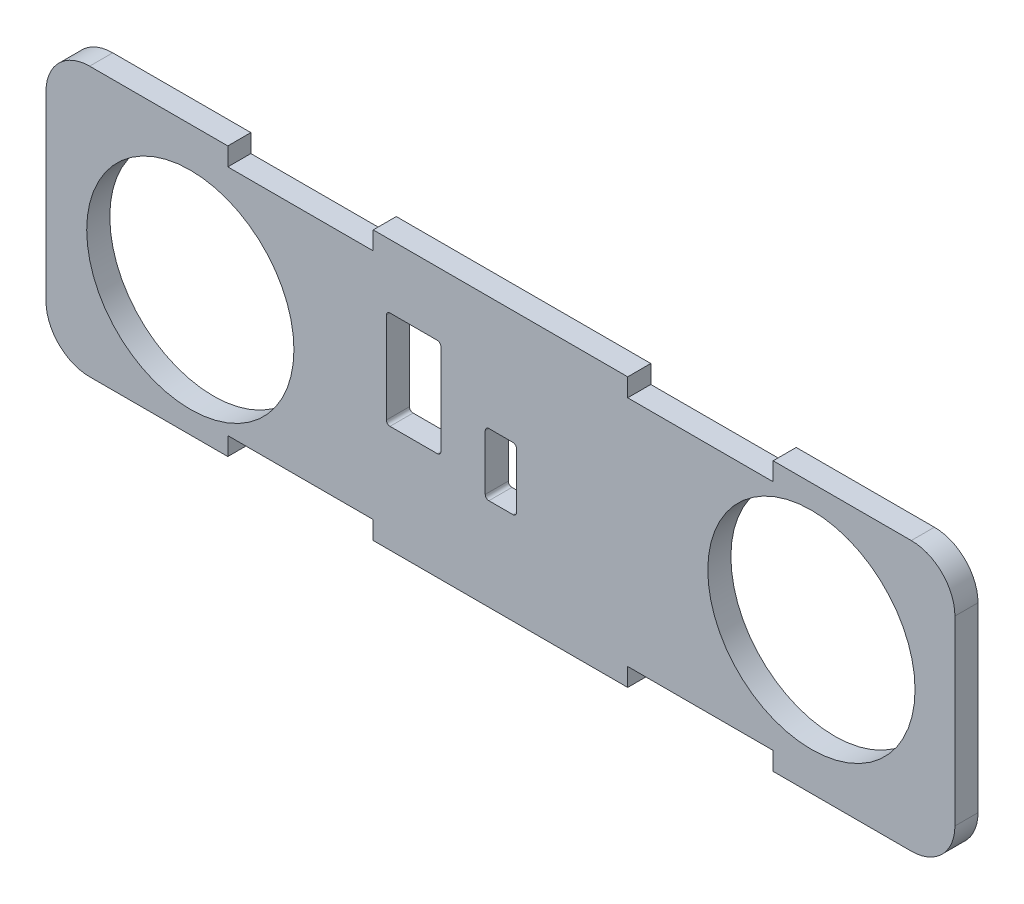
SolidWorks part; units mm, degrees
ref_plane "Front" through (0, 0, 0) normal (0, 0, 1) x (1, 0, 0)
ref_plane "Top" through (0, 0, 0) normal (0, 1, 0) x (1, 0, 0)
ref_plane "Right" through (0, 0, 0) normal (1, 0, 0) x (0, 0, -1)
sketch "Sketch1" plane through (0, 0, 0) normal (0, 0, 1) x (1, 0, 0)
  line L1 (-62.5, -18.5) -> (62.5, -18.5)
  line L2 (-62.5, -18.5) -> (-62.5, 18.5)
  line L3 (-62.5, 18.5) -> (62.5, 18.5)
  line L4 (62.5, -18.5) -> (62.5, 18.5)
  line L5 (-62.5, -18.5) -> (62.5, 18.5) construction
  line L6 (-62.5, 18.5) -> (62.5, -18.5) construction
  point P0 (0, 0)
  dimension "D1" = 37
  dimension "D2" = 125
extrude "Boss-Extrude1" add sketch "Sketch1" along normal blind 3.175
fillet "Fillet1" radius 6 4 edges at (-62.5, 18.5, 1.5875) (62.5, 18.5, 1.5875) (62.5, -18.5, 1.5875) (-62.5, -18.5, 1.5875)
sketch "Sketch2" plane through (0, 0, 3.175) normal (0, 0, 1) x (1, 0, 0)
  line L4 (-2.0937, 2.7963) -> (-1.3697, 2.7963) construction
  line L5 (2.2063, -5.8037) -> (1.4823, -5.8037) construction
  line L6 (2.2063, -5.8037) -> (2.2063, -5.4037) construction
  line L7 (-2.0937, 2.7963) -> (-2.0937, 2.3963) construction
  line L8 (-9.9037, -0.7737) -> (-13.9837, -0.7737) construction
  line L9 (-13.9837, 6.8463) -> (-9.9037, 6.8463) construction
  line L10 (-14.4837, 4.8063) -> (-14.4837, 6.3463) construction
  line L11 (-9.4037, 1.2663) -> (-9.4037, -0.2737) construction
  line L12 (-9.9037, -0.7737) -> (-13.9837, -0.7737) construction
  line L13 (-13.9837, 6.8463) -> (-9.9037, 6.8463) construction
  line L14 (-14.4837, 4.8063) -> (-14.4837, 6.3463) construction
  line L15 (-9.4037, 1.2663) -> (-9.4037, -0.2737) construction
  circle A0 centre (-42.6527, -1.2074) radius 13.5 construction
  circle A1 centre (-42.6527, -1.2074) radius 13.5 construction
  circle A2 centre (42.7653, 1) radius 13.5 construction
  circle A3 centre (42.7653, 1) radius 13.5 construction
sketch "Sketch3" plane through (0, 0, 3.175) normal (0, 0, 1) x (1, 0, 0)
  line L0 (-9.4037, -0.2737) -> (-9.4037, -0.8386) construction
  line L1 (-9.4037, 6.8463) -> (-14.4837, -0.8386) construction
  line L2 (-14.4837, 6.3463) -> (-14.4837, 6.8463) construction
  line L3 (-13.9837, 6.8463) -> (-14.4837, 6.8463) construction
  line L5 (-9.4037, -0.8386) -> (-14.4837, -0.8386) construction
  line L6 (-9.4037, -0.8386) -> (-9.4037, 6.8463) construction
  line L7 (-9.4037, 6.8463) -> (-14.4837, 6.8463) construction
  line L8 (-14.4837, -0.8386) -> (-14.4837, 6.8463) construction
  line L9 (2.2063, -5.8037) -> (-2.0937, -5.8037)
  line L10 (2.2063, -5.8037) -> (2.2063, 2.7963)
  line L11 (2.2063, 2.7963) -> (-2.0937, 2.7963)
  line L12 (-2.0937, -5.8037) -> (-2.0937, 2.7963)
  line L13 (-8.1937, 9.7538) -> (-15.6937, 9.7538)
  line L14 (-8.1937, 9.7538) -> (-8.1937, -3.7462)
  line L15 (-8.1937, -3.7462) -> (-15.6937, -3.7462)
  line L16 (-15.6937, 9.7538) -> (-15.6937, -3.7462)
  line L17 (-8.1937, 9.7538) -> (-15.6937, -3.7462) construction
  line L18 (-8.1937, -3.7462) -> (-15.6937, 9.7538) construction
  circle A0 centre (42.7653, 1) radius 14.25
  circle A1 centre (-42.6527, -1.2074) radius 14.25
  point P7 (-11.9437, 3.0038)
  dimension "D1" = 28.5
  dimension "D2" = 28.5
  dimension "D3" = 13.5
  dimension "D4" = 7.5
extrude "Cut-Extrude1" cut sketch "Sketch3" against normal up to next
sketch "Sketch4" plane through (0, 0, 3.175) normal (0, 0, 1) x (1, 0, 0)
  line L0 (57.3, 16) -> (37.5, 16) construction
  line L1 (57.3, 16) -> (37.5, 16) construction
  line L2 (-57.3, -16) -> (-37.5, -16) construction
  line L3 (-57.3, -16) -> (-37.5, -16) construction
sketch "Sketch6" plane through (0, 0, 3.175) normal (0, 0, 1) x (1, 0, 0)
  line L0 (-57.3, -16) -> (59.076, -16) construction
  line L1 (57.3, 16) -> (-57.1109, 16) construction
  line L2 (37.5, -16) -> (37.5, -18.5)
  line L3 (-56.5, -18.5) -> (56.5, -18.5) construction
  line L4 (62.5, -12.5) -> (62.5, 12.5) construction
  line L5 (37.5, -18.5) -> (17.5, -18.5)
  line L6 (17.5, -18.5) -> (17.5, -16)
  line L7 (17.5, -16) -> (37.5, -16)
  line L8 (0, 0) -> (-21.4026, 0) construction
  line L9 (0, 0) -> (0, -23.3465) construction
  line L10 (-17.5, -16) -> (-37.5, -16)
  line L11 (-17.5, -18.5) -> (-17.5, -16)
  line L12 (-37.5, -18.5) -> (-17.5, -18.5)
  line L13 (-37.5, -16) -> (-37.5, -18.5)
  line L14 (-37.5, 16) -> (-37.5, 18.5)
  line L15 (-37.5, 18.5) -> (-17.5, 18.5)
  line L16 (-17.5, 18.5) -> (-17.5, 16)
  line L17 (-17.5, 16) -> (-37.5, 16)
  line L18 (17.5, 16) -> (37.5, 16)
  line L19 (17.5, 18.5) -> (17.5, 16)
  line L20 (37.5, 18.5) -> (17.5, 18.5)
  line L21 (37.5, 16) -> (37.5, 18.5)
  dimension "D1" = 25
  dimension "D2" = 20
extrude "Cut-Extrude2" cut sketch "Sketch6" against normal through all
fillet "Fillet2" radius 0.5 8 edges at (-2.0937, 2.7963, 1.5875) (2.2063, 2.7963, 1.5875) (2.2063, -5.8037, 1.5875) (-2.0937, -5.8037, 1.5875) (-8.1937, 9.7538, 1.5875) (-15.6937, 9.7538, 1.5875) (-8.1937, -3.7462, 1.5875) (-15.6937, -3.7462, 1.5875)
equation "\"joystick opening\"= 28.5"
equation "\"D1@Sketch3\"=\"joystick opening\""
equation "\"D2@Sketch3\"= \"joystick opening\""
